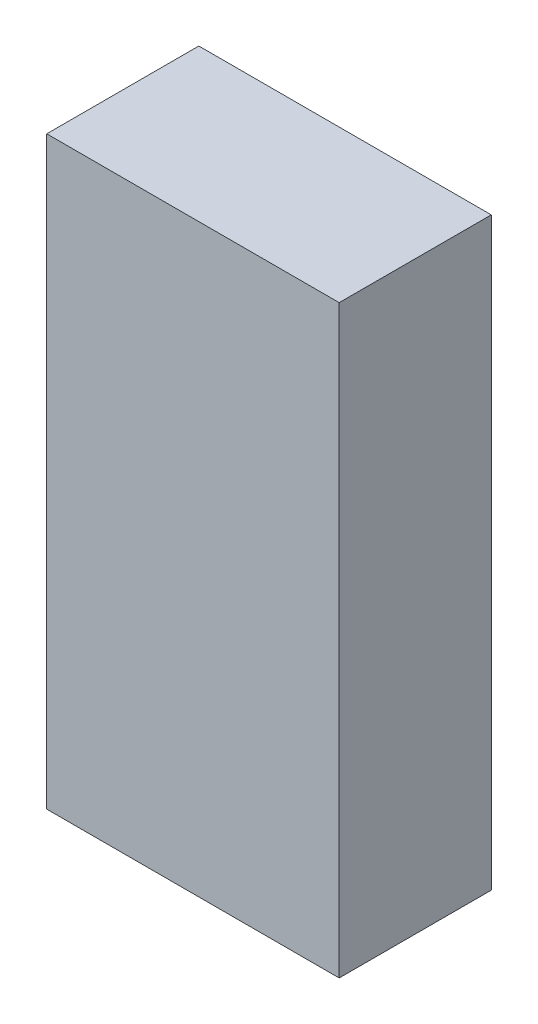
SolidWorks part; units mm, degrees
ref_plane "Front Plane" through (0, 0, 0) normal (0, 0, 1) x (1, 0, 0)
ref_plane "Top Plane" through (0, 0, 0) normal (0, 1, 0) x (1, 0, 0)
ref_plane "Right Plane" through (0, 0, 0) normal (1, 0, 0) x (0, 0, -1)
sketch "Sketch2" plane through (0, 0, 0) normal (0, 1, 0) x (1, 0, 0)
  line L1 (-11.1437, 15.9573) -> (-6.1437, 15.9573)
  line L2 (-11.1437, 15.9573) -> (-11.1437, 13.3573)
  line L3 (-11.1437, 13.3573) -> (-6.1437, 13.3573)
  line L4 (-6.1437, 15.9573) -> (-6.1437, 13.3573)
  line L5 (-11.1437, 15.9573) -> (-6.1437, 13.3573) construction
  line L6 (-11.1437, 13.3573) -> (-6.1437, 15.9573) construction
  point P0 (-8.6437, 14.6573)
  dimension "D1" = 5
  dimension "D2" = 2.6
extrude "Boss-Extrude1" add sketch "Sketch2" along normal blind 10
